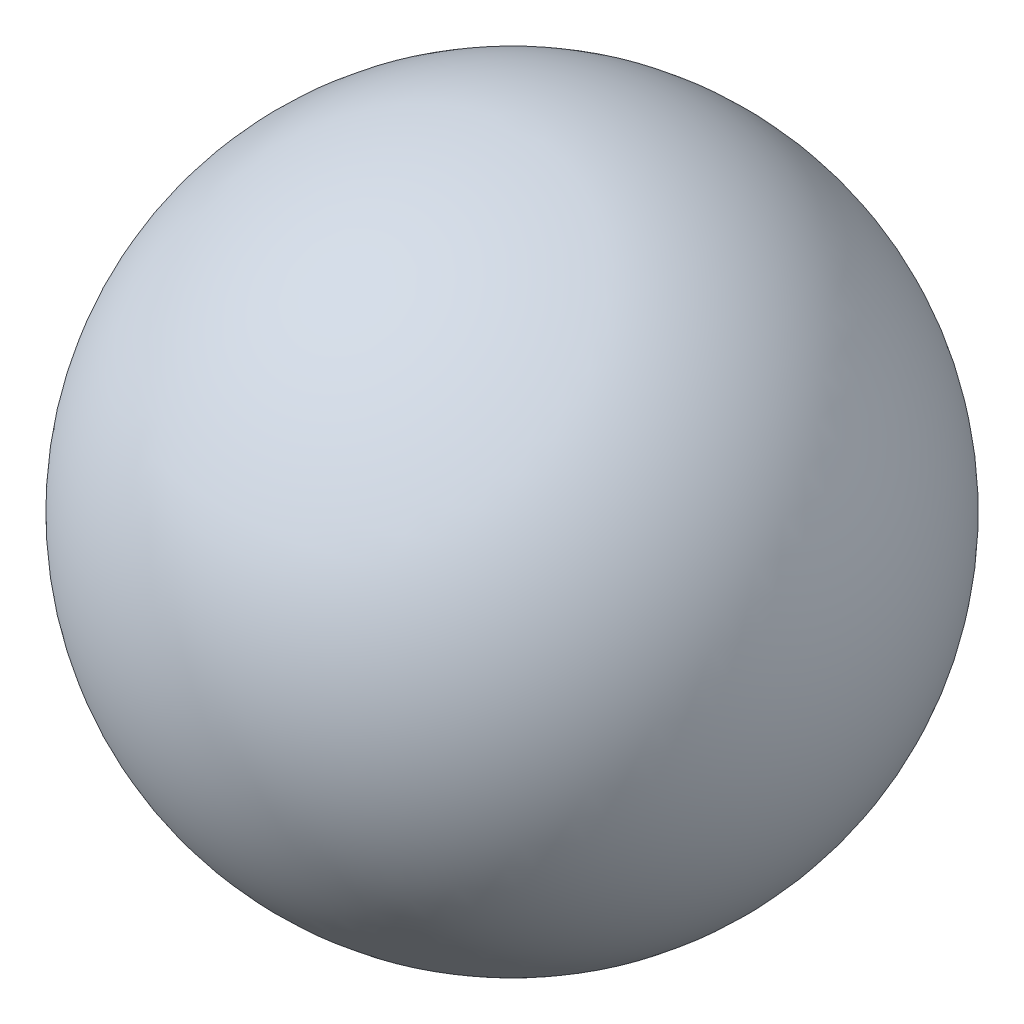
SolidWorks part; units mm, degrees
material "Polyurethane Foam Flexible"
ref_plane "Front Plane" through (0, 0, 0) normal (0, 0, 1) x (1, 0, 0)
ref_plane "Top Plane" through (0, 0, 0) normal (0, 1, 0) x (1, 0, 0)
ref_plane "Right Plane" through (0, 0, 0) normal (1, 0, 0) x (0, 0, -1)
sketch "Sketch2" plane through (0, 0, 0) normal (0, 0, 1) x (1, 0, 0)
  line L0 (0, 88.9) -> (0, -88.9)
  arc A0 (0, 88.9) -> (0, -88.9) centre (0, 0) ccw
  dimension "D1" = 88.9
revolve "Revolve1" add sketch "Sketch2" angle 360 about L0
